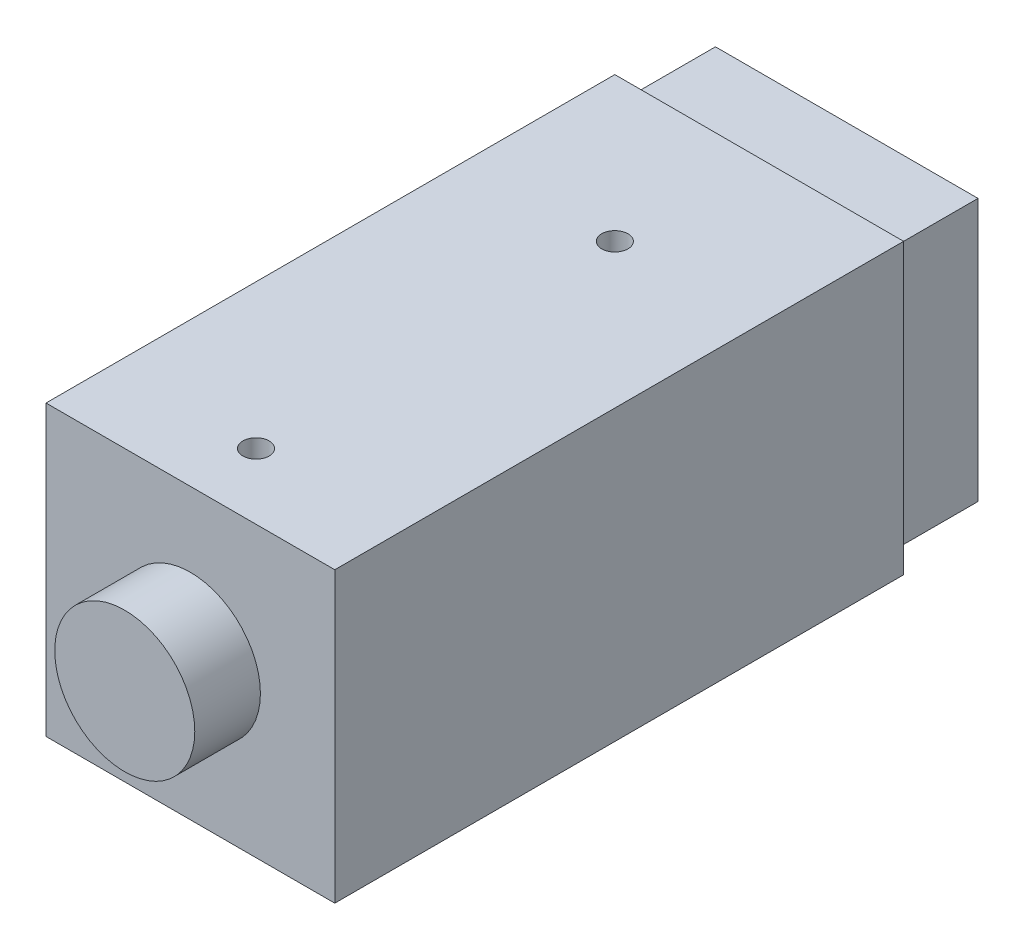
SolidWorks part; units mm, degrees
material "AISI 1020"
ref_plane "Plano frontal" through (0, 0, 0) normal (0, 0, 1) x (1, 0, 0)
ref_plane "Plano superior" through (0, 0, 0) normal (0, 1, 0) x (1, 0, 0)
ref_plane "Plano direito" through (0, 0, 0) normal (1, 0, 0) x (0, 0, -1)
sketch "Esboço1" plane through (0, 0, 0) normal (0, 0, 1) x (1, 0, 0)
  line L1 (-16.5, 16.5) -> (16.5, 16.5)
  line L2 (-16.5, 16.5) -> (-16.5, -16.5)
  line L3 (-16.5, -16.5) -> (16.5, -16.5)
  line L4 (16.5, 16.5) -> (16.5, -16.5)
  line L5 (-16.5, 16.5) -> (16.5, -16.5) construction
  line L6 (-16.5, -16.5) -> (16.5, 16.5) construction
  point P0 (0, 0)
  dimension "D1" = 33
extrude "Ressalto-extrusão1" add sketch "Esboço1" along normal blind 65
sketch "Esboço2" plane through (0, 0, 0) normal (0, 0, -1) x (-1, 0, 0)
  line L1 (-15, 15) -> (15, 15)
  line L2 (-15, 15) -> (-15, -15)
  line L3 (-15, -15) -> (15, -15)
  line L4 (15, 15) -> (15, -15)
  line L5 (-15, 15) -> (15, -15) construction
  line L6 (-15, -15) -> (15, 15) construction
  point P0 (0, 0)
  dimension "D1" = 30
extrude "Ressalto-extrusão2" add sketch "Esboço2" along normal blind 10
sketch "Esboço3" plane through (0, 0, 65) normal (0, 0, 1) x (1, 0, 0)
  circle A0 centre (0, 0) radius 8
  dimension "D1" = 16
extrude "Ressalto-extrusão3" add sketch "Esboço3" along normal blind 7.5
sketch "Esboço4" plane through (0, 16.5, 0) normal (0, 1, 0) x (1, 0, 0)
  line L0 (16.5, 0) -> (-16.5, 0) construction
  line L2 (16.5, -65) -> (-16.5, -65) construction
  circle A0 centre (0, -16.5) radius 1.5
  circle A1 centre (0, -57.5) radius 1.5
  point P6 (0, 0)
  point P9 (0, -65)
  dimension "D1" = 15
  dimension "D2" = 3
  dimension "D3" = 38
extrude "Corte-extrusão1" cut sketch "Esboço4" against normal blind 7.5
